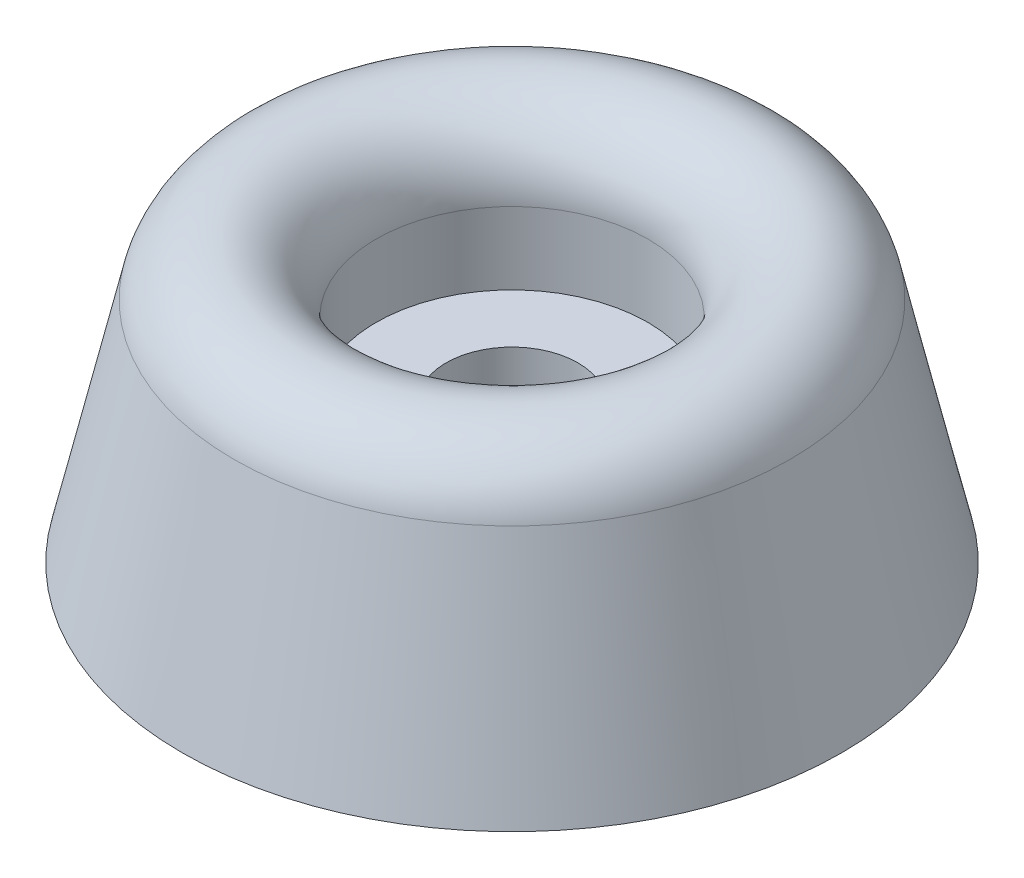
SolidWorks part; units mm, degrees
ref_plane "Front Plane" through (0, 0, 0) normal (0, 0, 1) x (1, 0, 0)
ref_plane "Top Plane" through (0, 0, 0) normal (0, 1, 0) x (1, 0, 0)
ref_plane "Right Plane" through (0, 0, 0) normal (1, 0, 0) x (0, 0, -1)
sketch "Sketch1" plane through (0, 0, 0) normal (0, 0, 1) x (1, 0, 0)
  line L0 (0, 0) -> (0, 10.668) construction
  line L1 (0, 0) -> (12.3825, 0) construction
  line L2 (0, 0) -> (0, 5.2578) construction
  line L3 (0, 5.2578) -> (5.1054, 5.2578) construction
  line L4 (5.1054, 5.2578) -> (5.1054, 10.668) construction
  line L5 (0, 10.668) -> (12.3825, 10.668) construction
  line L6 (12.3825, 10.668) -> (12.3825, 0) construction
  line L7 (10.5029, 10.668) -> (10.5029, 0) construction
  line L8 (0, 7.5438) -> (12.3825, 7.5438) construction
  line L9 (10.4358, 8.5672) -> (12.3825, 0)
  line L10 (5.1054, 7.9693) -> (5.1054, 5.2578)
  line L11 (5.1054, 5.2578) -> (2.4765, 5.2578)
  line L12 (2.4765, 5.2578) -> (2.4765, 0)
  line L13 (2.4765, 0) -> (12.3825, 0)
  arc A0 (10.4358, 8.5672) -> (5.1054, 7.9693) centre (7.8041, 7.9693) ccw
  dimension "D1" = 10.668
  dimension "D2" = 12.3825
  dimension "D3" = 5.1054
  dimension "D4" = 5.2578
  dimension "D5" = 10.5029
  dimension "D6" = 7.5438
  dimension "D7" = 2.4765
revolve "Revolve1" add sketch "Sketch1" angle 360 about L2
